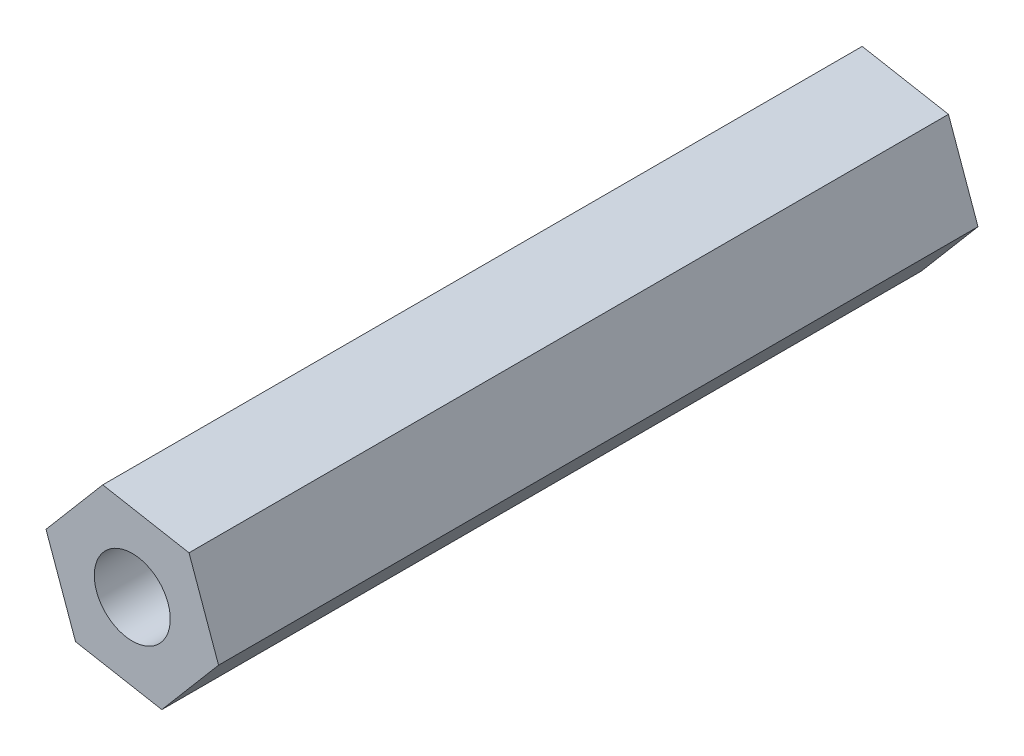
SolidWorks part; units mm, degrees
material "ABS"
ref_plane "Plano frontal" through (0, 0, 0) normal (0, 0, 1) x (1, 0, 0)
ref_plane "Plano superior" through (0, 0, 0) normal (0, 1, 0) x (1, 0, 0)
ref_plane "Plano direito" through (0, 0, 0) normal (1, 0, 0) x (0, 0, -1)
sketch "Esboço1" plane through (0, 0, 0) normal (0, 0, 1) x (1, 0, 0)
  line L1 (12.9332, -4.1439) -> (9.5251, -3.5237)
  line L2 (9.5251, -3.5237) -> (7.2839, -6.1651)
  line L3 (7.2839, -6.1651) -> (8.4508, -9.4267)
  line L4 (8.4508, -9.4267) -> (11.8589, -10.0469)
  line L5 (11.8589, -10.0469) -> (14.1001, -7.4055)
  line L6 (14.1001, -7.4055) -> (12.9332, -4.1439)
  circle A0 centre (10.692, -6.7853) radius 3 construction
extrude "Ressalto-extrusão1" add sketch "Esboço1" along normal blind 30
sketch "Esboço4" plane through (0, 0, 0) normal (0, 0, -1) x (-1, 0, 0)
  line L1 (-12.9332, -4.1439) -> (-9.5251, -3.5237) construction
  circle A0 centre (-10.692, -6.7853) radius 1.5
  dimension "D1" = 3
extrude "Corte-extrusão2" cut sketch "Esboço4" against normal blind 40
